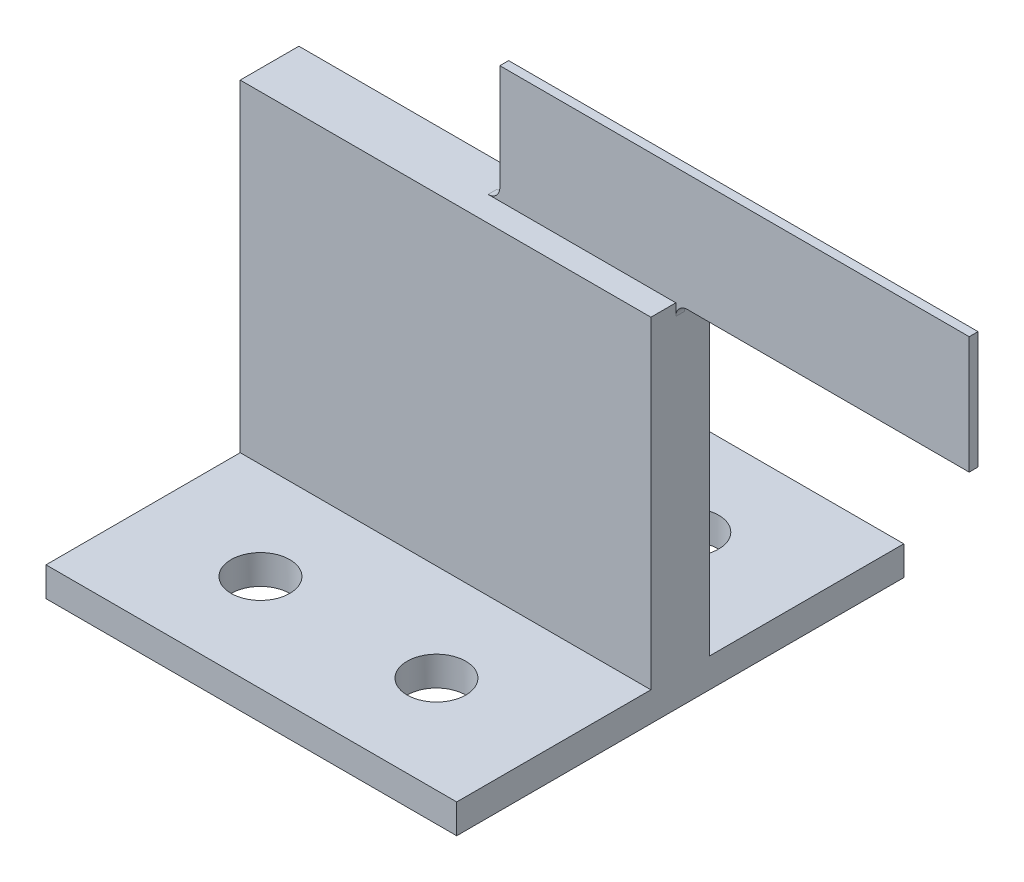
SolidWorks part; units mm, degrees
ref_plane "Plan de face" through (0, 0, 0) normal (0, 0, 1) x (1, 0, 0)
ref_plane "Plan de dessus" through (0, 0, 0) normal (0, 1, 0) x (1, 0, 0)
ref_plane "Plan de droite" through (0, 0, 0) normal (1, 0, 0) x (0, 0, -1)
sketch "Esquisse1" plane through (0, 0, 0) normal (0, 1, 0) x (1, 0, 0)
  line L1 (17.5, -2.5) -> (-17.5, -2.5)
  line L2 (17.5, -2.5) -> (17.5, 2.5)
  line L3 (17.5, 2.5) -> (-17.5, 2.5)
  line L4 (-17.5, -2.5) -> (-17.5, 2.5)
  line L5 (17.5, -2.5) -> (-17.5, 2.5) construction
  line L6 (17.5, 2.5) -> (-17.5, -2.5) construction
  point P0 (0, 0)
  dimension "D1" = 35
  dimension "D2" = 5
extrude "Boss.-Extru.1" add sketch "Esquisse1" along normal blind 30
sketch "Esquisse2" plane through (0, 30, 0) normal (0, 1, 0) x (1, 0, 0)
  line L1 (42.5, -0.375) -> (2.5, -0.375)
  line L2 (42.5, -0.375) -> (42.5, 0.375)
  line L3 (42.5, 0.375) -> (2.5, 0.375)
  line L4 (2.5, -0.375) -> (2.5, 0.375)
  line L5 (42.5, -0.375) -> (2.5, 0.375) construction
  line L6 (42.5, 0.375) -> (2.5, -0.375) construction
  line L8 (17.5, -2.5) -> (17.5, 2.5) construction
  point P0 (22.5, 0)
  point P7 (17.5, 0)
  dimension "D1" = 40
  dimension "D2" = 0.75
  dimension "D3" = 5
extrude "Boss.-Extru.2" add sketch "Esquisse2" along normal blind 10
fillet "Congé1" radius 1 2 edges at (2.5, 30, 0) (17.5, 30, 0)
sketch "Esquisse3" plane through (0, 0, 0) normal (0, -1, 0) x (1, 0, 0)
  line L0 (-17.5, -2.5) -> (-17.5, 2.5) construction
  line L1 (17.5, -19.05) -> (-17.5, -19.05)
  line L2 (17.5, -19.05) -> (17.5, 19.05)
  line L3 (17.5, 19.05) -> (-17.5, 19.05)
  line L4 (-17.5, -19.05) -> (-17.5, 19.05)
  line L5 (17.5, -19.05) -> (-17.5, 19.05) construction
  line L6 (17.5, 19.05) -> (-17.5, -19.05) construction
  point P0 (0, 0)
  dimension "D1" = 38.1
extrude "Boss.-Extru.3" add sketch "Esquisse3" against normal blind 2.5
sketch "Esquisse4" plane through (0, 2.5, 0) normal (0, 1, 0) x (1, 0, 0)
  line L0 (17.5, 19.05) -> (17.5, 2.5) construction
  line L1 (-22, 0) -> (22, 0) construction
  line L3 (-17.5, 2.5) -> (-17.5, 19.05) construction
  circle A1 centre (-7.5, 10.775) radius 2.5
  circle A2 centre (7.5, 10.775) radius 2.5
  circle A3 centre (7.5, -10.775) radius 2.5
  circle A4 centre (-7.5, -10.775) radius 2.5
  point P10 (17.5, 10.775)
  dimension "D1" = 5
  dimension "D2" = 10
  dimension "D3" = 15
extrude "Enlèv. mat.-Extru.1" cut sketch "Esquisse4" against normal up to surface (2.5 mm away) up to face at (0, 0, 0)
